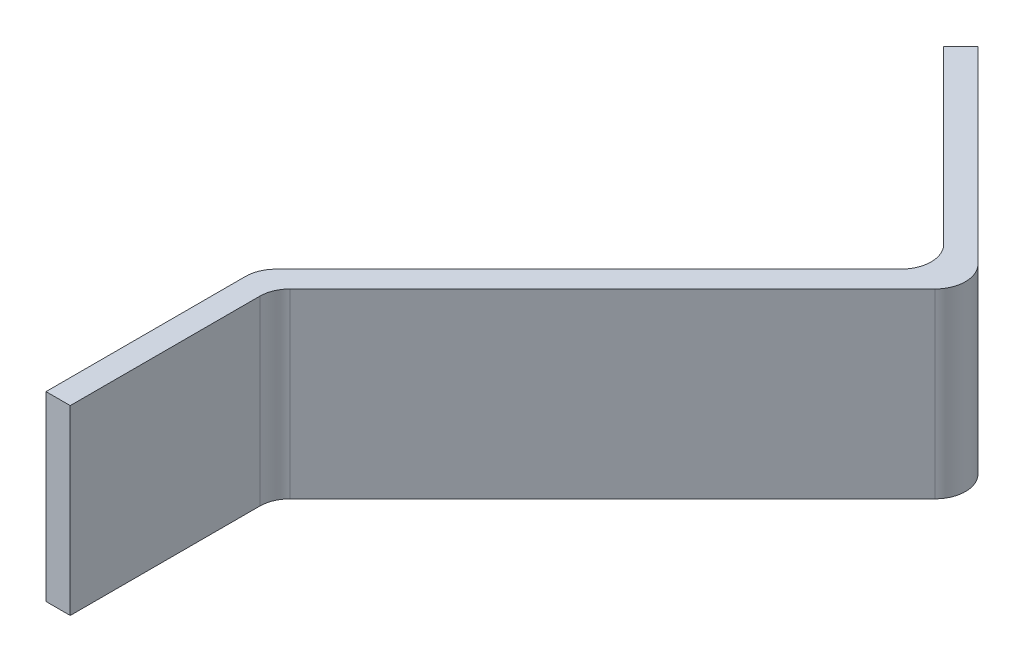
SolidWorks part; units mm, degrees
ref_plane "Front Plane" through (0, 0, 0) normal (0, 0, 1) x (1, 0, 0)
ref_plane "Top Plane" through (0, 0, 0) normal (0, 1, 0) x (1, 0, 0)
ref_plane "Right Plane" through (0, 0, 0) normal (1, 0, 0) x (0, 0, -1)
ref_plane "Plane1" through (0, 7.5, 0) normal (0, 1, 0) x (1, 0, 0)
sketch "Sketch1" plane through (0, 7.5, 0) normal (0, 1, 0) x (1, 0, 0)
  line B0 (248.7921, 471.7609) -> (217.6794, 502.8736)
  line B1 (217.6794, 502.8736) -> (214.851, 500.0452)
  line B2 (214.851, 500.0452) -> (243.1353, 471.7609)
  line B3 (243.1353, 464.6899) -> (191.5667, 413.1213)
  line B4 (190.1023, 409.5858) -> (190.1023, 376.6569)
  line B5 (190.1023, 376.6569) -> (194.1023, 376.6569)
  line B6 (194.1023, 376.6569) -> (194.1023, 407.9289)
  line B7 (195.5667, 411.4645) -> (248.7921, 464.6899)
  arc B8 (248.7921, 464.6899) -> (248.7921, 471.7609) centre (245.2566, 468.2254) ccw
  arc B9 (243.1353, 464.6899) -> (243.1353, 471.7609) centre (239.5997, 468.2254) ccw
  arc B10 (191.5667, 413.1213) -> (190.1023, 409.5858) centre (195.1023, 409.5858) ccw
  arc B11 (195.5667, 411.4645) -> (194.1023, 407.9289) centre (199.1023, 407.9289) ccw
sketch_block_instance "Block1-1"
sketch_block "Block1" parameters "D1"=0
extrude "Boss-Extrude1" add sketch "Sketch1" against normal blind 30
